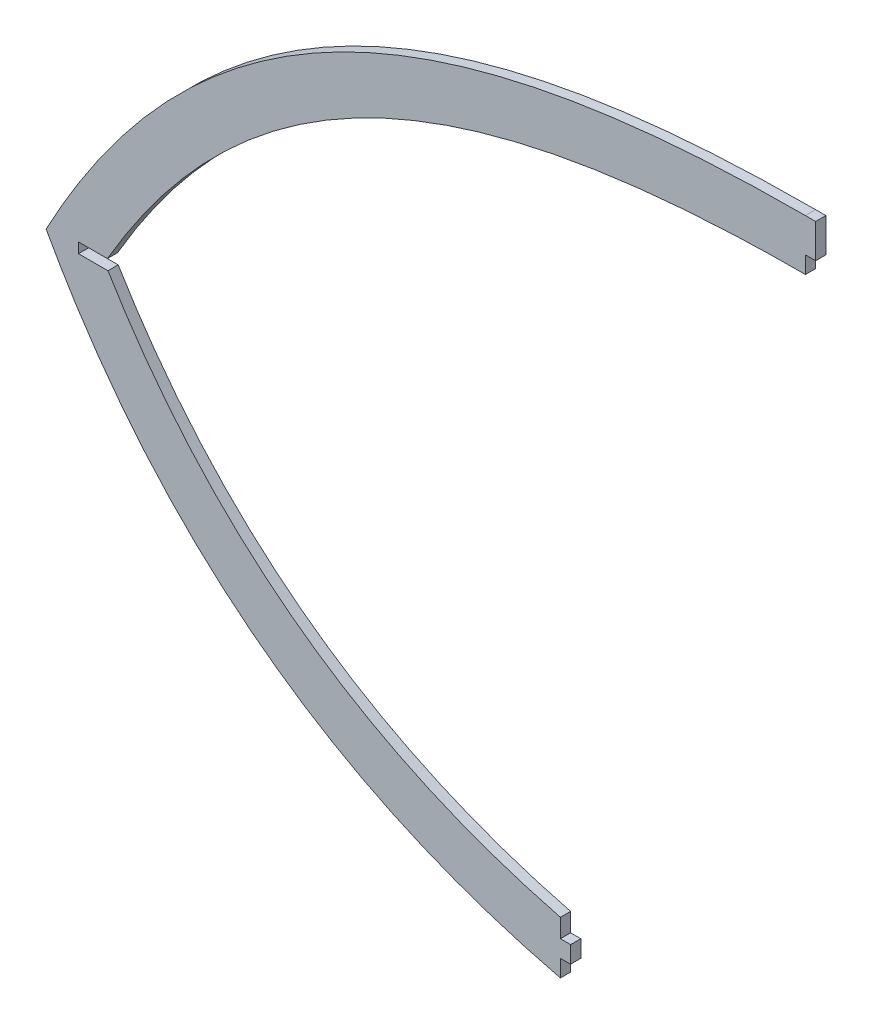
SolidWorks part; units mm, degrees
material "birch 3mm plywood"
ref_plane "Front" through (0, 0, 0) normal (0, 0, 1) x (1, 0, 0)
ref_plane "Top" through (0, 0, 0) normal (0, 1, 0) x (1, 0, 0)
ref_plane "Right" through (0, 0, 0) normal (1, 0, 0) x (0, 0, -1)
sketch "Sketch1" plane through (0, 0, 0) normal (0, 0, 1) x (1, 0, 0)
  line L1 (-83, 160.5) -> (-83, -69.5) construction
  line L2 (-83, 150.5) -> (-80, 150.5)
  line L3 (-80, 150.5) -> (-83, 150.5) construction
  line L4 (-155, -69.5) -> (-155, -64.5)
  line L6 (-155, -69.5) -> (-155, 44) construction
  line L9 (-155, -64.5) -> (-152, -64.5)
  line L12 (-152, -64.5) -> (-152, -59.5)
  line L13 (-152, -59.5) -> (-155, -59.5)
  line L14 (-155, -59.5) -> (-155, -54.0482)
  line L15 (-288.0952, 47) -> (-296.5952, 47)
  line L16 (-83, 47) -> (-305.0917, 47) construction
  line L17 (-296.5952, 47) -> (-296.5952, 44)
  line L18 (-305.0917, 44) -> (-83, 44) construction
  line L19 (-296.5952, 44) -> (-287.9228, 44)
  line L20 (-83, 160.5) -> (-83, 150.5) construction
  line L21 (-83, 160.5) -> (-80, 160.5)
  line L22 (-80, 160.5) -> (-80, 150.5)
  line L23 (-83, 150.5) -> (-83, 145.5)
  line L24 (-155, 43.3771) -> (-155, -69.5) construction
  line L25 (-152, -69.5) -> (-152, 43.3771) construction
  parabola Q0 (-155, -69.5) -> (-306.0893, 45.5) focus (-179.0197, 57.3821) apex (-244.7409, -27.552) construction
  parabola Q1 (-155, -69.5) -> (-306.0893, 45.5) focus (-179.0197, 57.3821) apex (-244.7409, -27.552)
  spline S0 degree 3 poles (912.6271, 67.093) (-173.2309, 29.6899) (-479.3533, 668.8854) (-333.6092, -954.1027) knots -1.973203 -1.973203 -1.973203 -1.973203 2.60577 2.60577 2.60577 2.60577 only from (-83, 160.5) to (-306.0893, 45.5) construction
  spline S1 degree 3 poles (-83, 160.5) (-186.6749, 160.5) (-259.8996, 132.37) (-306.0893, 45.5) knots 0 0 0 0 1 1 1 1
  spline S2 degree 1 poles (-151.4967, -54.9148) (-288.8909, 45.6217) knots 0 0 1 1 construction
  spline S3 degree 1 poles (-83, 145.5) (-288.8909, 45.6217) knots 0 0 1 1 construction
  spline S4 degree 3 poles (-151.4967, -54.9148) (-153.3988, -54.458) (-157.2086, -53.4983) (-164.6601, -51.4419) (-173.7484, -48.594) (-184.2693, -44.7413) (-197.7998, -39.024) (-213.7896, -30.7928) (-231.5494, -19.1756) (-247.9291, -5.7971) (-260.462, 6.8492) (-269.8307, 17.8876) (-276.5289, 26.6314) (-281.8406, 34.3147) (-285.9211, 40.691) (-287.9161, 43.9748) (-288.8909, 45.6217) knots 0.497669 0.497669 0.497669 0.497669 0.497806 0.497943 0.498217 0.498491 0.498765 0.499314 0.499862 0.500411 0.500959 0.501233 0.501508 0.501782 0.501919 0.502056 0.502056 0.502056 0.502056 only from (-155, -54.0482) to (-287.9228, 44)
  spline S5 degree 3 poles (-288.8909, 45.6217) (-288.2118, 46.8068) (-286.8274, 49.1771) (-284.0331, 53.7809) (-280.4563, 59.3452) (-276.0412, 65.7051) (-269.9863, 73.7792) (-262.1032, 83.1283) (-252.1296, 93.2247) (-241.6235, 102.2655) (-226.87, 112.9967) (-206.9505, 124.0773) (-184.8372, 132.3478) (-165.7316, 137.4023) (-150.6813, 140.4388) (-134.8993, 142.7481) (-121.1337, 144.0897) (-109.751, 144.8283) (-101.0301, 145.2187) (-93.6051, 145.4111) (-87.5802, 145.4874) (-84.523, 145.5) (-83, 145.5) knots 0 0 0 0 0.015161 0.030323 0.060645 0.090968 0.12129 0.181936 0.242581 0.303226 0.363871 0.485162 0.606452 0.667098 0.727743 0.788388 0.849033 0.879356 0.909679 0.940001 0.955163 0.970324 0.970324 0.970324 0.970324 only from (-288.0952, 47) to (-83, 145.5)
  dimension "D3" = 5
  dimension "D4" = 5
  dimension "D5" = 8.5
  dimension "D1" = 15
extrude "Boss-Extrude1" add sketch "Sketch1" along normal mid plane 3 contours S1 Q1 L4 L9 L12 L13 L14 S4 L19 L17 L15 S5 L23 L2 L22 L21
